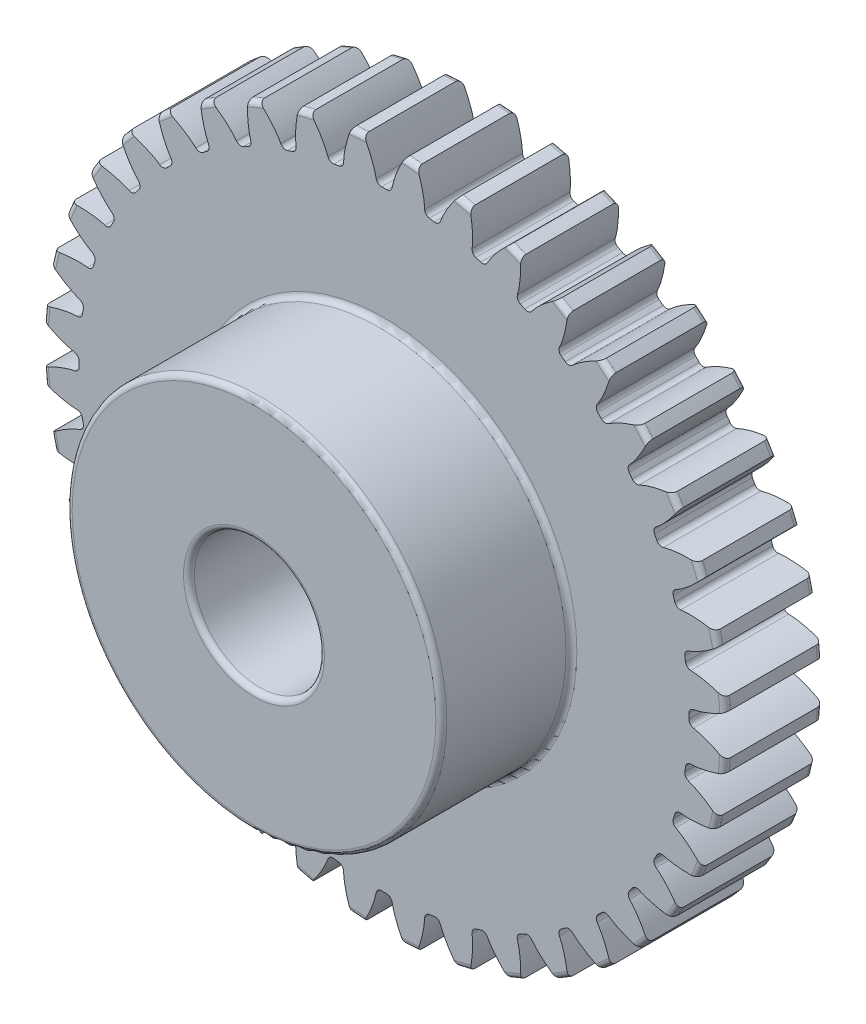
SolidWorks part; units mm, degrees
ref_plane "Front Plane" through (0, 0, 0) normal (0, 0, 1) x (1, 0, 0)
ref_plane "Top Plane" through (0, 0, 0) normal (0, 1, 0) x (1, 0, 0)
ref_plane "Right Plane" through (0, 0, 0) normal (1, 0, 0) x (0, 0, -1)
sketch "Sketch1" plane through (0, 0, 0) normal (0, 0, 1) x (1, 0, 0)
  line L0 (0, 0) -> (0, 15.875) construction
  line L1 (-5.1021, 17.732) -> (5.1021, 14.018) construction
  circle A0 centre (0, 0) radius 14.8828 construction
  circle A1 centre (0, 0) radius 16.6687 construction
  circle A2 centre (0, 0) radius 15.875 construction
  circle A3 centre (0, 0) radius 14.9176 construction
  circle A4 centre (0, 0) radius 3.175 construction
  circle A5 centre (0, 0) radius 9.144 construction
  point P8 (406.4, 0)
  point P13 (508, 0)
  dimension "OD | Outside Diameter" = 33.3375
  dimension "Root Diameter" = 29.7656
  dimension "Gear Pitch Diameter" = 31.75
  dimension "Base Diameter" = 29.8352
  dimension "For Shaft Diameter" = 6.35
  dimension "Hub Diameter" = 18.288
  dimension "Pressure Angle" = 20
  dimension "Number of Teeth" = 1016
  dimension "Gear Pitch | Diametral Pitch" = 812.8
sketch "Sketch2" plane through (0, 0, 0) normal (1, 0, 0) x (0, 0, -1)
  line L0 (-5.5626, 0) -> (5.5626, 0) construction
  line L1 (-5.5626, 16.6687) -> (5.5626, 16.6688) construction
  point P2 (0, 16.6687)
  point P4 (0.7874, 0)
  point P6 (0.7874, 16.6687)
  dimension "Overall Width" = 11.1252
  dimension "Hub Width" = 6.35
  dimension "Face Width" = 4.7752
sketch "Sketch3" plane through (0, 0, 0) normal (0, 0, 1) x (1, 0, 0)
  circle A0 centre (0, 0) radius 16.6687
  circle A1 centre (0, 0) radius 16.6687 construction
extrude "Boss-Extrude1" add sketch "Sketch3" against normal up to vertex (5.5626 mm away) and the other way up to vertex (5.5626 mm away) up to point (0, 0, -5.5626) other way up to point (0, 0, 5.5626)
sketch "Sketch5" plane through (0, 0, 0) normal (1, 0, 0) x (0, 0, -1)
  line L1 (-5.5626, 16.6687) -> (0.7874, 16.6687)
  line L2 (-5.5626, 16.6687) -> (-5.5626, 9.144)
  line L3 (-5.5626, 9.144) -> (0.7874, 9.144)
  line L4 (0.7874, 16.6687) -> (0.7874, 9.144)
  line L11 (5.5626, 3.175) -> (-5.5626, 3.175)
  line L12 (5.5626, 3.175) -> (5.5626, 0)
  line L13 (5.5626, 0) -> (-5.5626, 0)
  line L14 (-5.5626, 3.175) -> (-5.5626, 0)
  point P5 (0, 3.175)
  point P12 (0, 9.144)
revolve "Cut-Revolve1" cut sketch "Sketch5" angle 360 about L0
fillet "Fillet2" radius 0.2663 6 edges at (16.6687, 0, -5.5626) (3.175, 0, -5.5626) (3.175, 0, 5.5626) (9.144, 0, -0.7874) (16.6687, 0, -0.7874) (9.144, 0, 5.5626)
sketch "Sketch4" plane through (0, 0, 0) normal (0, 0, 1) x (1, 0, 0)
  line L0 (0, 0) -> (14.8784, 0.3626) construction
  line L2 (0, 0) -> (14.8784, -0.3626) construction
  line L4 (14.8784, 0.3626) -> (14.9132, 0.3634)
  line L5 (14.9132, -0.3634) -> (14.8784, -0.3626)
  arc A0 (14.8784, 0.3626) -> (14.8784, -0.3626) centre (0, 0) cw
  arc A3 (16.6383, 1.0067) -> (16.6383, -1.0067) centre (0, 0) cw
  circle A4 centre (0, 0) radius 16.6687 construction
  spline S0 degree 4 poles (14.9132, 0.3634) (14.9159, 0.3635) (14.9236, 0.3639) (14.9381, 0.3649) (14.9618, 0.3671) (14.9919, 0.3706) (15.0308, 0.376) (15.0766, 0.3835) (15.1268, 0.3928) (15.1814, 0.4042) (15.2358, 0.4166) (15.29, 0.4301) (15.3439, 0.4444) (15.4091, 0.4628) (15.4872, 0.4863) (15.5783, 0.516) (15.6814, 0.5524) (15.7862, 0.5921) (15.8891, 0.6335) (15.9927, 0.678) (16.0929, 0.7228) (16.1965, 0.7721) (16.2921, 0.8189) (16.3988, 0.8743) (16.4848, 0.9199) (16.5978, 0.9832) (16.6645, 1.0215) (16.7423, 1.0675) (16.7768, 1.0885) (16.798, 1.1014) knots 0 0 0 0 0 0.005377 0.015084 0.028532 0.04661 0.064855 0.092111 0.119476 0.146842 0.174209 0.201575 0.228941 0.256307 0.307035 0.361767 0.4165 0.471232 0.525964 0.580697 0.635429 0.690161 0.744894 0.799626 0.854358 0.909091 0.954545 1 1 1 1 1 construction
  spline S1 degree 4 poles (14.9132, 0.3634) (14.9159, 0.3635) (14.9236, 0.3639) (14.9381, 0.3649) (14.9618, 0.3671) (14.9919, 0.3706) (15.0308, 0.376) (15.0766, 0.3835) (15.1268, 0.3928) (15.1814, 0.4042) (15.2358, 0.4166) (15.29, 0.4301) (15.3439, 0.4444) (15.4091, 0.4628) (15.4872, 0.4863) (15.5783, 0.516) (15.6814, 0.5524) (15.7862, 0.5921) (15.8891, 0.6335) (15.9927, 0.678) (16.0929, 0.7228) (16.1965, 0.7721) (16.2921, 0.8189) (16.3988, 0.8743) (16.4848, 0.9199) (16.5733, 0.9695) (16.6163, 0.994) (16.6383, 1.0067) knots 0 0 0 0 0 0.005377 0.015084 0.028532 0.04661 0.064855 0.092111 0.119476 0.146842 0.174209 0.201575 0.228941 0.256307 0.307035 0.361767 0.4165 0.471232 0.525964 0.580697 0.635429 0.690161 0.744894 0.799626 0.854358 0.909091 0.909091 0.909091 0.909091 0.909091
  spline S2 degree 4 poles (14.9132, -0.3634) (14.9159, -0.3635) (14.9236, -0.3639) (14.9381, -0.3649) (14.9618, -0.3671) (14.9919, -0.3706) (15.0308, -0.376) (15.0766, -0.3835) (15.1268, -0.3928) (15.1814, -0.4042) (15.2358, -0.4166) (15.29, -0.4301) (15.3439, -0.4444) (15.4091, -0.4628) (15.4872, -0.4863) (15.5783, -0.516) (15.6814, -0.5524) (15.7862, -0.5921) (15.8891, -0.6335) (15.9927, -0.678) (16.0929, -0.7228) (16.1965, -0.7721) (16.2921, -0.8189) (16.3988, -0.8743) (16.4848, -0.9199) (16.5978, -0.9832) (16.6645, -1.0215) (16.7423, -1.0675) (16.7768, -1.0885) (16.798, -1.1014) knots 0 0 0 0 0 0.005377 0.015084 0.028532 0.04661 0.064855 0.092111 0.119476 0.146842 0.174209 0.201575 0.228941 0.256307 0.307035 0.361767 0.4165 0.471232 0.525964 0.580697 0.635429 0.690161 0.744894 0.799626 0.854358 0.909091 0.954545 1 1 1 1 1 construction
  spline S3 degree 4 poles (14.9132, -0.3634) (14.9159, -0.3635) (14.9236, -0.3639) (14.9381, -0.3649) (14.9618, -0.3671) (14.9919, -0.3706) (15.0308, -0.376) (15.0766, -0.3835) (15.1268, -0.3928) (15.1814, -0.4042) (15.2358, -0.4166) (15.29, -0.4301) (15.3439, -0.4444) (15.4091, -0.4628) (15.4872, -0.4863) (15.5783, -0.516) (15.6814, -0.5524) (15.7862, -0.5921) (15.8891, -0.6335) (15.9927, -0.678) (16.0929, -0.7228) (16.1965, -0.7721) (16.2921, -0.8189) (16.3988, -0.8743) (16.4848, -0.9199) (16.5733, -0.9695) (16.6163, -0.994) (16.6383, -1.0067) knots 0 0 0 0 0 0.005377 0.015084 0.028532 0.04661 0.064855 0.092111 0.119476 0.146842 0.174209 0.201575 0.228941 0.256307 0.307035 0.361767 0.4165 0.471232 0.525964 0.580697 0.635429 0.690161 0.744894 0.799626 0.854358 0.909091 0.909091 0.909091 0.909091 0.909091
  dimension "D1" = 29.7656
extrude "Cut-Extrude1" cut sketch "Sketch4" against normal through all both and the other way through all
fillet "Fillet1" radius 0.2663 2 edges at (14.8784, -0.3626, -3.175) (14.8784, 0.3626, -3.175)
pattern_circular "CirPattern1" count 40 over 360 about axis through (0, 0, 5.5626) along (0, 0, -1) of "Cut-Extrude1", "Fillet1"
equation "\"Root Diameter@Sketch1\"=\"Root Diameter\""
equation "\"OD | Outside Diameter@Sketch1\"=\"Outside Diameter\""
equation "\"D1@CirPattern1\"=\"Number of Teeth\""
equation "\"Diametral Pitch\"=32"
equation "\"Number of Teeth\"= 40"
equation "\"Pressure Angle\"=20"
equation "\"Pitch Diameter\"= \"Number of Teeth\" / \"Diametral Pitch\""
equation "\"Base Diameter\"= \"Pitch Diameter\" * cos ( \"Pressure Angle\" )"
equation "\"Outside Diameter\"= ( \"Number of Teeth\" + 2 ) / \"Diametral Pitch\""
equation "\"Dedendum\"= 1.25 / \"Diametral Pitch\""
equation "\"Root Diameter\"= \"Pitch Diameter\" - ( 2 * \"Dedendum\" )"
equation "\"Pitch Angle\"= 360deg / \"Number of Teeth\""
equation "\"Alpha\"= sqr ( \"Pitch Diameter\" ^ 2 - \"Base Diameter\" ^ 2 ) / \"Base Diameter\" * 180 / PI - \"Pressure Angle\""
equation "\"Beta\"= ( \"Pitch Angle\" / 4 - \"Alpha\" )"
equation "\"Phi\"= sqr ( ( \"Outside Diameter\" / 2 ) ^ 2 - ( \"Base Diameter\" / 2 ) ^ 2 ) / ( \"Base Diameter\" / 2 )"
equation "\"Addendum\"= 1 / \"Diametral Pitch\""
equation "\"WorkingDepth\"= 2 / \"Diametral Pitch\""
equation "\"WholeDepth\"= 2.25 / \"Diametral Pitch\""
equation "\"Clearance\"= 0.25 / \"Diametral Pitch\""
equation "\"ToothThickness\"= ( pi * 2 ) / \"Diametral Pitch\""
equation "\"CircularPitch\"= pi / \"Diametral Pitch\""
equation "\"Number of Teeth@Sketch1\"=\"Number of Teeth\""
equation "\"Gear Pitch | Diametral Pitch@Sketch1\"=\"Diametral Pitch\""
equation "\"Pressure Angle@Sketch1\"=\"Pressure Angle\""
equation "\"Gear Pitch Diameter@Sketch1\"=\"Pitch Diameter\""
equation "\"Base Diameter@Sketch1\"=\"Base Diameter\""
equation "\"Fillet\"= \"Clearance\" * cos ( \"Pressure Angle\" ) * tan ( ( 90 + \"Pressure Angle\" ) / 2 )"
equation "\"D1@Fillet1\"=\"Fillet\""
equation "\"D1@Sketch4\"=if( \"Base Diameter\">\"Root Diameter\",\"Root Diameter\",\"Base Diameter\"-.00001)"
equation "\"D1@Fillet2\"=\"Fillet\""
